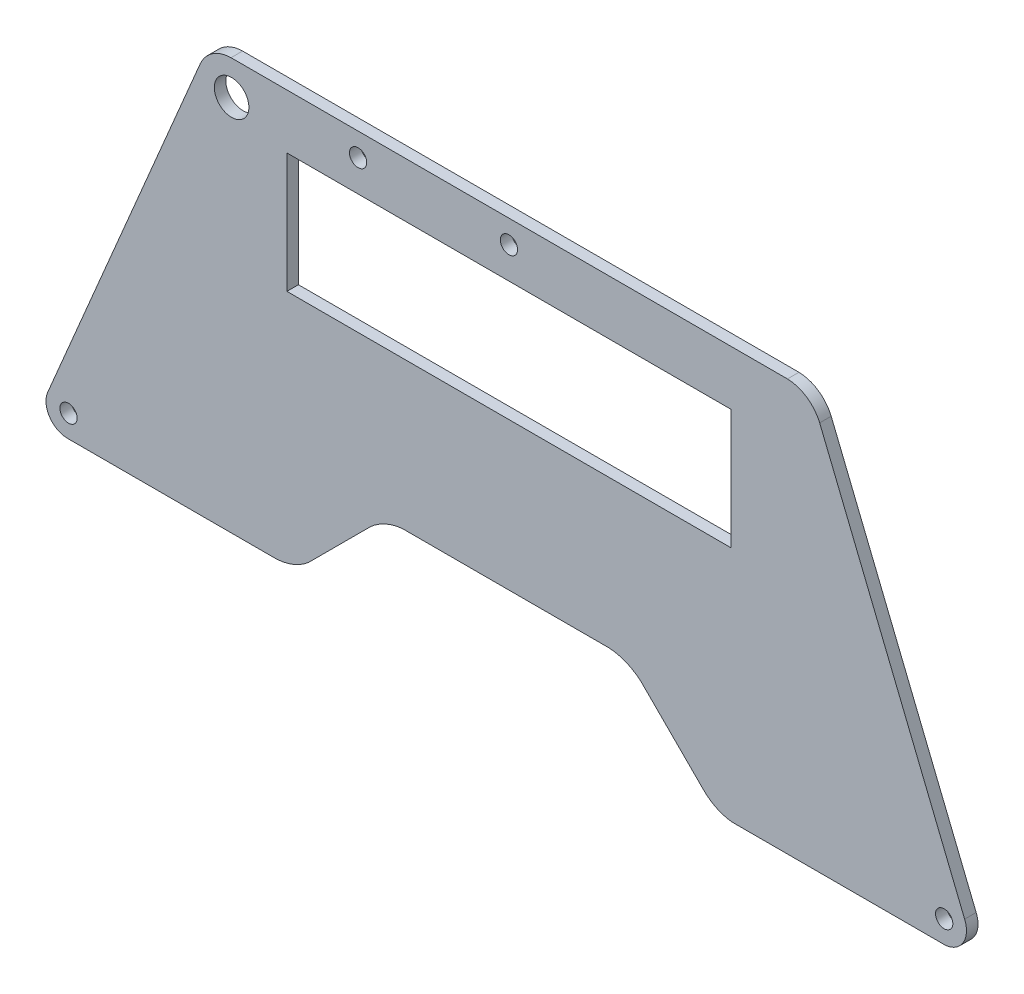
SolidWorks part; units mm, degrees
ref_plane "Plano frontal" through (0, 0, 0) normal (0, 0, 1) x (1, 0, 0)
ref_plane "Plano superior" through (0, 0, 0) normal (0, 1, 0) x (1, 0, 0)
ref_plane "Plano direito" through (0, 0, 0) normal (1, 0, 0) x (0, 0, -1)
sketch "Esboço1" plane through (0, 0, 0) normal (0, 0, 1) x (1, 0, 0)
  line L12 (-0.452, 5.715) -> (-25.598, 67.691)
  line L14 (-31.186, 71.501) -> (-127.706, 71.501)
  line L15 (-133.04, 67.945) -> (-159.456, 5.461)
  line L16 (-156.154, 0.127) -> (-119.832, 0.127)
  line L17 (-114.244, 2.413) -> (-103.576, 13.081)
  line L18 (-97.988, 15.621) -> (-62.174, 15.621)
  line L19 (-56.586, 13.335) -> (-45.918, 2.667)
  line L20 (-40.838, 0.127) -> (-3.754, 0.127)
  line L29 (-0.452, 5.715) -> (-25.598, 67.691)
  line L30 (-31.186, 71.501) -> (-127.706, 71.501)
  line L31 (-133.04, 67.945) -> (-159.456, 5.461)
  line L32 (-156.154, 0.127) -> (-119.832, 0.127)
  line L33 (-114.244, 2.413) -> (-103.576, 13.081)
  line L34 (-97.988, 15.621) -> (-62.174, 15.621)
  line L35 (-56.586, 13.335) -> (-45.918, 2.667)
  line L36 (-40.838, 0.127) -> (-3.754, 0.127)
  circle A25 centre (-127.6108, 65.5797) radius 2.9989
  circle A26 centre (-105.664, 67.501) radius 1.5
  circle A27 centre (-79.5, 67.501) radius 1.5
  circle A28 centre (-4, 4) radius 1.5
  circle A29 centre (-155.893, 4) radius 1.5
  arc A33 (-3.754, 0.127) -> (-0.452, 5.715) centre (-4.1512, 4.1313) ccw
  arc A34 (-25.598, 67.691) -> (-31.186, 71.501) centre (-31.3404, 65.2716) ccw
  arc A35 (-127.706, 71.501) -> (-133.04, 67.945) centre (-127.6108, 65.5797) ccw
  arc A36 (-159.456, 5.461) -> (-156.154, 0.127) centre (-156.0642, 3.8716) ccw
  arc A37 (-119.832, 0.127) -> (-114.244, 2.413) centre (-120.331, 9.3196) ccw
  arc A38 (-97.988, 15.621) -> (-103.576, 13.081) centre (-97.057, 6.1561) ccw
  arc A39 (-56.586, 13.335) -> (-62.174, 15.621) centre (-62.673, 6.4284) ccw
  arc A40 (-45.918, 2.667) -> (-40.838, 0.127) centre (-39.9485, 8.256) ccw
  arc A41 (-3.754, 0.127) -> (-0.452, 5.715) centre (-4.1512, 4.1313) ccw
  arc A42 (-25.598, 67.691) -> (-31.186, 71.501) centre (-31.3404, 65.2716) ccw
  arc A43 (-127.706, 71.501) -> (-133.04, 67.945) centre (-127.6108, 65.5797) ccw
  arc A44 (-159.456, 5.461) -> (-156.154, 0.127) centre (-156.0642, 3.8716) ccw
  arc A45 (-119.832, 0.127) -> (-114.244, 2.413) centre (-120.331, 9.3196) ccw
  arc A46 (-97.988, 15.621) -> (-103.576, 13.081) centre (-97.057, 6.1561) ccw
  arc A47 (-56.586, 13.335) -> (-62.174, 15.621) centre (-62.673, 6.4284) ccw
  arc A48 (-45.918, 2.667) -> (-40.838, 0.127) centre (-39.9485, 8.256) ccw
  dimension "D1" = 0
extrude "Ressalto-extrusão1" add sketch "Esboço1" along normal blind 2
sketch "Esboço3" plane through (0, 0, 0) normal (0, 0, -1) x (-1, 0, 0)
  line L9 (41.012, 41.2408) -> (118.012, 41.2408)
  line L10 (41.012, 41.2408) -> (41.012, 62.0408)
  line L11 (41.012, 62.0408) -> (118.012, 62.0408)
  line L12 (118.012, 41.2408) -> (118.012, 62.0408)
extrude "Corte-extrusão2" cut sketch "Esboço3" against normal through all
